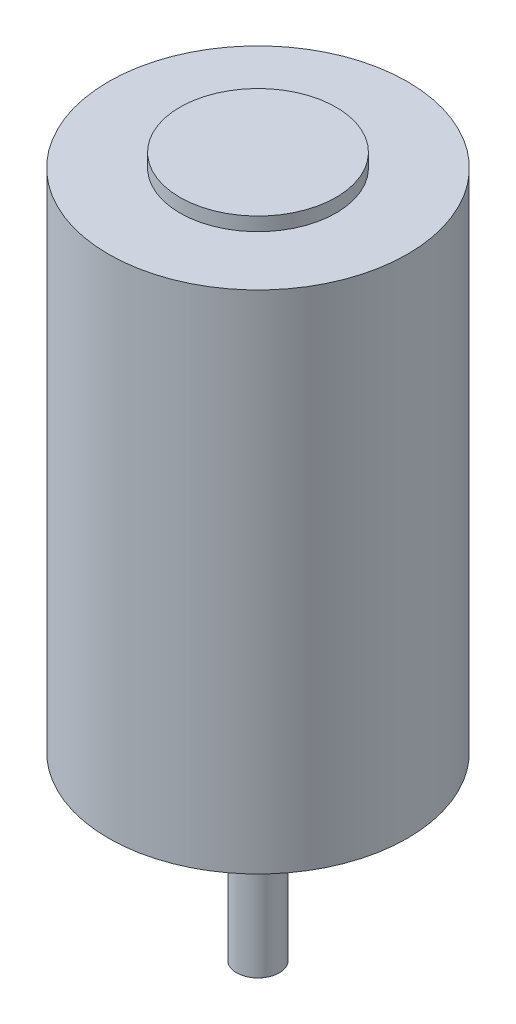
SolidWorks part; units mm, degrees
ref_plane "Front Plane" through (0, 0, 0) normal (0, 0, 1) x (1, 0, 0)
ref_plane "Top Plane" through (0, 0, 0) normal (0, 1, 0) x (1, 0, 0)
ref_plane "Right Plane" through (0, 0, 0) normal (1, 0, 0) x (0, 0, -1)
sketch "Sketch2" plane through (0, 0, 0) normal (0, 1, 0) x (1, 0, 0)
  circle A0 centre (0, 0) radius 21.0185
  dimension "D1" = 42.037
extrude "Boss-Extrude1" add sketch "Sketch2" along normal blind 71.12
sketch "Sketch3" plane through (0, 71.12, 0) normal (0, 1, 0) x (1, 0, 0)
  circle A0 centre (0, 0) radius 10.9855
  dimension "D1" = 21.971
extrude "Boss-Extrude2" add sketch "Sketch3" along normal blind 1.905
sketch "Sketch4" plane through (0, 0, 0) normal (0, -1, 0) x (1, 0, 0)
  circle A0 centre (0, 0) radius 10.9855
  circle A1 centre (0, 0) radius 8.4455
  dimension "D1" = 21.971
  dimension "D2" = 16.891
extrude "Boss-Extrude3" add sketch "Sketch4" along normal blind 1.905
sketch "Sketch5" plane through (0, 0, 0) normal (0, -1, 0) x (1, 0, 0)
  circle A0 centre (0, 0) radius 3
  dimension "D1" = 6
extrude "Boss-Extrude4" add sketch "Sketch5" along normal blind 25.4
sketch "Sketch6" plane through (0, 0, 0) normal (0, -1, 0) x (1, 0, 0)
  circle A0 centre (0, 0) radius 5.08
  dimension "D1" = 10.16
extrude "Boss-Extrude5" add sketch "Sketch6" along normal blind 3.429
sketch "Sketch7" plane through (0, 0, 0) normal (0, -1, 0) x (1, 0, 0)
  line L0 (0, 0) -> (0, 19.9779) construction
  circle A0 centre (16, 0) radius 1.27
  circle A1 centre (-16, 0) radius 1.27
  dimension "D1" = 2.54
  dimension "D2" = 16
extrude "Cut-Extrude1" cut sketch "Sketch7" against normal blind 5.08
